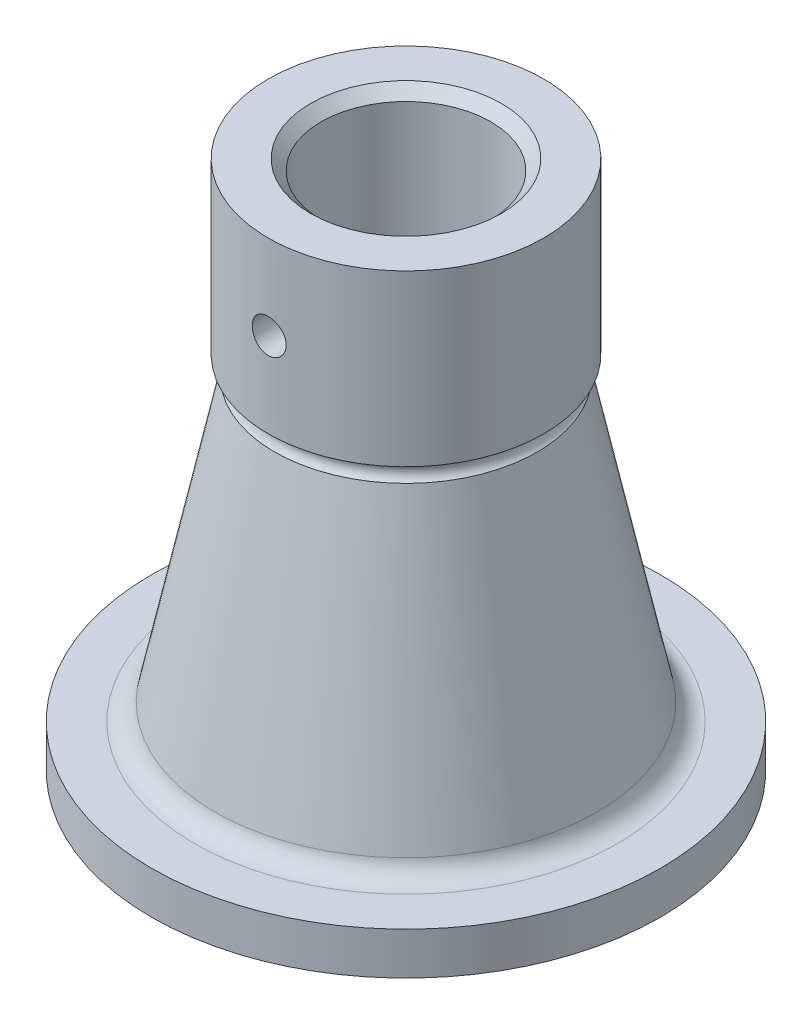
SolidWorks part; units mm, degrees
ref_plane "Front Plane" through (0, 0, 0) normal (0, 0, 1) x (1, 0, 0)
ref_plane "Top Plane" through (0, 0, 0) normal (0, 1, 0) x (1, 0, 0)
ref_plane "Right Plane" through (0, 0, 0) normal (1, 0, 0) x (0, 0, -1)
sketch "Sketch1" plane through (0, 0, 0) normal (0, 0, 1) x (1, 0, 0)
  line L0 (0, 107.6379) -> (0, -109.1956) construction
  line L1 (40, 250) -> (65, 250)
  line L2 (65, 250) -> (65, 170)
  line L3 (61.9406, 161.0453) -> (90, 27.9373)
  line L4 (99.785, 20) -> (120, 20)
  line L5 (120, 20) -> (120, 0)
  line L6 (120, 0) -> (80, 0)
  line L7 (80, 0) -> (45, 166.0325)
  line L8 (40, 170) -> (40, 250)
  line L9 (-123.692, 0) -> (223.572, 0) construction
  arc A0 (65, 170) -> (61.9406, 161.0453) centre (65, 165) ccw
  arc A1 (90, 27.9373) -> (99.785, 20) centre (99.785, 30) ccw
  arc A2 (45, 166.0325) -> (40, 170) centre (40.1075, 165.0012) ccw
  dimension "D3" = 5
  dimension "D4" = 10
  dimension "D8" = 5
  dimension "D1" = 130
  dimension "D2" = 80
  dimension "D5" = 150
  dimension "D6" = 20
  dimension "D7" = 160
  dimension "D9" = 90
  dimension "D10" = 80
  dimension "D11" = 240
  dimension "D12" = 180
revolve "Revolve1" add sketch "Sketch1" angle 360 about L0
chamfer "Chamfer1" distance 5 angle 45 1 edges at (-40, 250, 0)
sketch "Sketch2" plane through (0, 0, 0) normal (0, 0, 1) x (1, 0, 0)
  line L0 (0, 303.5124) -> (0, -55.4423) construction
  line L1 (65, 250) -> (-65, 250) construction
  circle A0 centre (0, 210) radius 8
  dimension "D1" = 16
  dimension "D2" = 40
extrude "Cut-Extrude1" cut sketch "Sketch2" along normal blind 120
